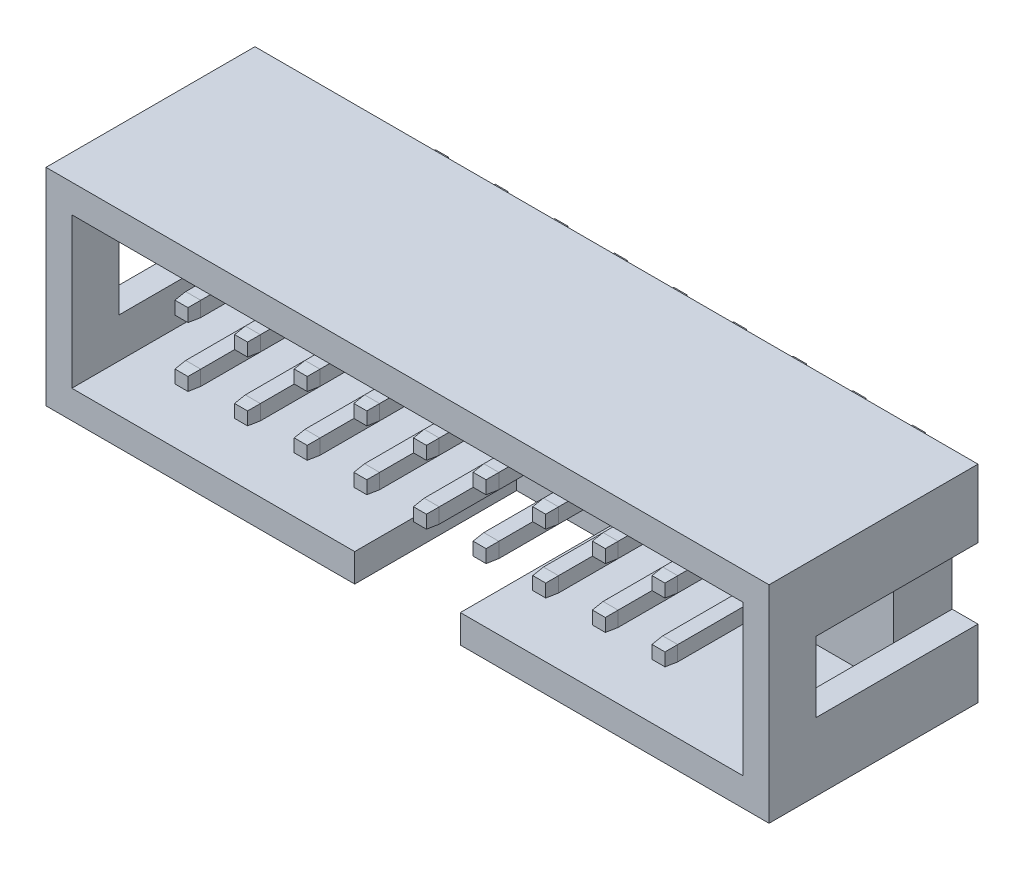
SolidWorks part; units mm, degrees
ref_plane "Front Plane" through (0, 0, 0) normal (0, 0, 1) x (1, 0, 0)
ref_plane "Top Plane" through (0, 0, 0) normal (0, 1, 0) x (1, 0, 0)
ref_plane "Right Plane" through (0, 0, 0) normal (1, 0, 0) x (0, 0, -1)
sketch "Sketch1" plane through (0, 0, 0) normal (0, 0, 1) x (1, 0, 0)
  line L1 (-21.7298, 4.6702) -> (9.0702, 4.6702)
  line L2 (-21.7298, 4.6702) -> (-21.7298, -4.1298)
  line L3 (-21.7298, -4.1298) -> (9.0702, -4.1298)
  line L4 (9.0702, 4.6702) -> (9.0702, -4.1298)
  dimension "D1" = 8.8
  dimension "D2" = 30.8
extrude "Boss-Extrude1" add sketch "Sketch1" along normal blind 2.5
sketch "Sketch2" plane through (0, 0, 2.5) normal (0, 0, 1) x (1, 0, 0)
  line L0 (-21.7298, 0.2702) -> (9.0702, 0.2702) construction
  line L1 (-21.7298, 4.6702) -> (9.0702, 4.6702)
  line L2 (-21.7298, 4.6702) -> (-21.7298, -4.1298)
  line L3 (-21.7298, -4.1298) -> (9.0702, -4.1298)
  line L4 (9.0702, 4.6702) -> (9.0702, -4.1298)
  line L6 (-20.6298, 3.4702) -> (7.9702, 3.4702)
  line L7 (-20.6298, 3.4702) -> (-20.6298, -2.9298)
  line L8 (-20.6298, -2.9298) -> (7.9702, -2.9298)
  line L9 (7.9702, 3.4702) -> (7.9702, -2.9298)
  line L10 (-20.6298, 3.4702) -> (7.9702, -2.9298) construction
  line L11 (-20.6298, -2.9298) -> (7.9702, 3.4702) construction
  point P8 (-6.3298, 0.2702)
  dimension "D1" = 1.1
  dimension "D2" = 1.2
extrude "Boss-Extrude2" add sketch "Sketch2" along normal blind 6.4
sketch "Sketch4" plane through (0, 0, 8.9) normal (0, 0, 1) x (1, 0, 0)
  line L0 (-21.7298, -4.1298) -> (9.0702, -4.1298) construction
  line L1 (-20.6298, -2.9298) -> (7.9702, -2.9298) construction
  line L2 (-8.5798, -2.9298) -> (-4.0798, -2.9298)
  line L3 (-8.5798, -2.9298) -> (-8.5798, -4.1298)
  line L4 (-8.5798, -4.1298) -> (-4.0798, -4.1298)
  line L5 (-4.0798, -2.9298) -> (-4.0798, -4.1298)
  point P10 (-6.3298, -4.1298)
  point P11 (-6.3298, -2.9298)
  point P12 (-4.0798, -3.5298)
  dimension "D1" = 4.5
extrude "Cut-Extrude1" cut sketch "Sketch4" against normal blind 6.9
sketch "Sketch5" plane through (0, 0, 0) normal (0, 0, -1) x (-1, 0, 0)
  line L0 (21.7298, 4.6702) -> (21.7298, -4.1298) construction
  line L1 (21.7298, 1.7702) -> (20.6298, 1.7702)
  line L2 (21.7298, 1.7702) -> (21.7298, -1.2298)
  line L3 (21.7298, -1.2298) -> (20.6298, -1.2298)
  line L4 (20.6298, 1.7702) -> (20.6298, -1.2298)
  line L5 (21.7298, 4.6702) -> (21.7298, -4.1298) construction
  line L6 (-9.0702, 4.6702) -> (-9.0702, -4.1298) construction
  line L8 (-9.0702, 1.7702) -> (-7.9702, 1.7702)
  line L9 (-9.0702, 1.7702) -> (-9.0702, -1.2298)
  line L10 (-9.0702, -1.2298) -> (-7.9702, -1.2298)
  line L11 (-7.9702, 1.7702) -> (-7.9702, -1.2298)
  point P8 (21.7298, 0.2702)
  point P9 (20.6298, 0.2702)
  point P20 (-9.0702, 0.2702)
  point P21 (-7.9702, 0.2702)
  dimension "D1" = 1.1
  dimension "D2" = 3
  dimension "D3" = 1.1
  dimension "D4" = 3
extrude "Cut-Extrude2" cut sketch "Sketch5" against normal blind 6.9
sketch "Sketch6" plane through (0, 0, 2.5) normal (0, 0, 1) x (1, 0, 0)
  line L0 (-21.7298, 4.6702) -> (-21.7298, -4.1298) construction
  line L1 (-16.9798, 1.8602) -> (-16.3398, 1.8602)
  line L2 (-16.9798, 1.8602) -> (-16.9798, 1.2202)
  line L3 (-16.9798, 1.2202) -> (-16.3398, 1.2202)
  line L4 (-16.3398, 1.8602) -> (-16.3398, 1.2202)
  line L5 (-16.9798, 1.8602) -> (-16.3398, 1.2202) construction
  line L6 (-16.9798, 1.2202) -> (-16.3398, 1.8602) construction
  line L7 (-16.6598, 1.5402) -> (-16.6598, -0.9998) construction
  line L8 (-16.9798, -0.6798) -> (-16.3398, -0.6798)
  line L9 (-16.9798, -0.6798) -> (-16.9798, -1.3198)
  line L10 (-16.9798, -1.3198) -> (-16.3398, -1.3198)
  line L11 (-16.3398, -0.6798) -> (-16.3398, -1.3198)
  line L12 (-16.9798, -0.6798) -> (-16.3398, -1.3198) construction
  line L13 (-16.9798, -1.3198) -> (-16.3398, -0.6798) construction
  line L16 (-20.6298, 1.7702) -> (-20.6298, -1.2298) construction
  point P0 (-16.6598, 1.5402)
  point P7 (-16.6598, -0.9998)
  point P12 (-16.6598, 0.2702)
  point P17 (-20.6298, 0.2702)
  dimension "D1" = 0.64
  dimension "D2" = 0.64
  dimension "D3" = 5.07
  dimension "D4" = 0.64
  dimension "D5" = 0.64
  dimension "D6" = 2.54
extrude "Boss-Extrude4" add sketch "Sketch6" along normal blind 5.7 and the other way blind 5.4
chamfer "Chamfer1" distance 0.5 angle 5 4 edges at (-16.6598, 1.8602, 8.2) (-16.3398, 1.5402, 8.2) (-16.6598, 1.2202, 8.2) (-16.9798, 1.5402, 8.2)
chamfer "Chamfer2" distance 0.5 angle 5 4 edges at (-16.6598, -0.6798, 8.2) (-16.3398, -0.9998, 8.2) (-16.6598, -1.3198, 8.2) (-16.9798, -0.9998, 8.2)
chamfer "Chamfer4" distance 0.5 angle 5 4 edges at (-16.6598, 1.8602, -2.9) (-16.9798, 1.5402, -2.9) (-16.6598, 1.2202, -2.9) (-16.3398, 1.5402, -2.9)
chamfer "Chamfer5" distance 0.5 angle 5 4 edges at (-16.6598, -0.6798, -2.9) (-16.9798, -0.9998, -2.9) (-16.6598, -1.3198, -2.9) (-16.3398, -0.9998, -2.9)
pattern_linear "LPattern1" count 9 spacing 2.54 along (1, 0, 0) of "Boss-Extrude4", "Chamfer1", "Chamfer2", "Chamfer4", "Chamfer5"
sketch "Sketch7" plane through (0, 0, -2.9) normal (0, 0, -1) x (-1, 0, 0)
  line L0 (-3.3839, 1.2639) -> (-3.9364, 1.8164) construction
  line L1 (-3.3839, 1.8164) -> (-3.9364, 1.2639) construction
  point P8 (-3.6602, 1.5402)
ref_plane "Plane1" through (3.6602, 0, 0) normal (1, 0, 0) x (0, 0, -1)
sketch "Sketch8" plane through (3.6602, 0, 0) normal (1, 0, 0) x (0, 0, -1)
  line L0 (2.9, 1.5402) -> (6.7616, 1.5402) construction
equation "\"Pitch\"= 2.54"
equation "\"NOC\"= 10"
equation "\"D2@Sketch1\"=\"Pitch\" * \"NOC\" + 5.4"
equation "\"D1@LPattern1\"=\"NOC\" - 1"
